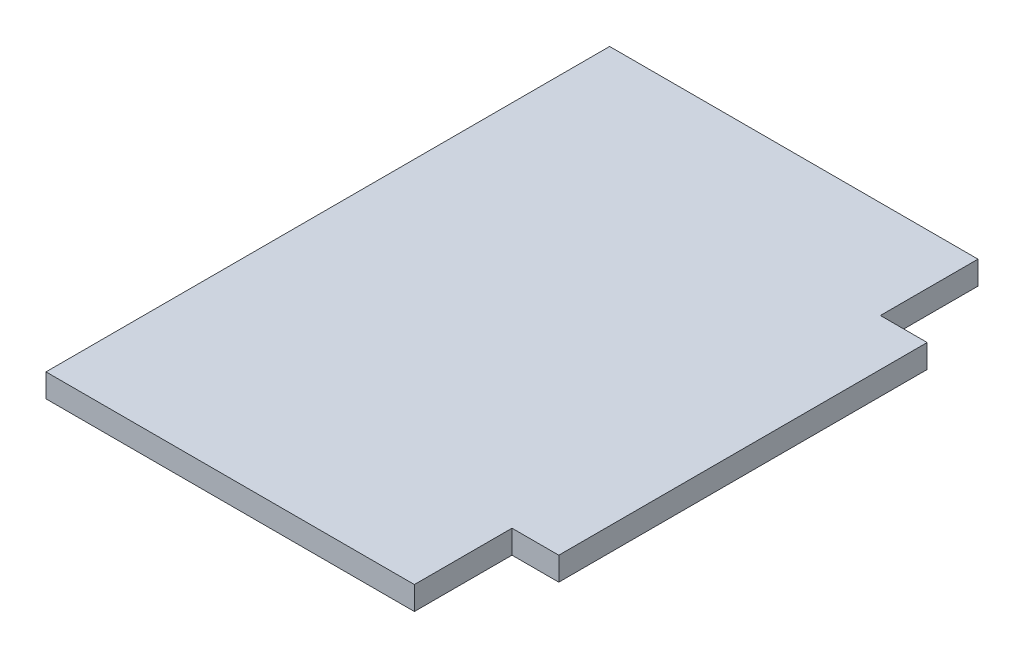
SolidWorks part; units mm, degrees
material "Cedar"
ref_plane "Front Plane" through (0, 0, 0) normal (0, 0, 1) x (1, 0, 0)
ref_plane "Top Plane" through (0, 0, 0) normal (0, 1, 0) x (1, 0, 0)
ref_plane "Right Plane" through (0, 0, 0) normal (1, 0, 0) x (0, 0, -1)
sketch "Sketch1" plane through (0, 0, 0) normal (0, 1, 0) x (1, 0, 0)
  line L0 (-25, 13.25) -> (25, 13.25)
  line L1 (25, 13.25) -> (25, 0)
  line L2 (25, 0) -> (31.35, 0)
  line L3 (31.35, 0) -> (31.35, -50)
  line L4 (31.35, -50) -> (25, -50)
  line L5 (25, -50) -> (25, -63.25)
  line L6 (25, -63.25) -> (-25, -63.25)
  line L7 (-25, -63.25) -> (-25, -50)
  line L8 (-25, -50) -> (-31.35, -50)
  line L9 (-31.35, -50) -> (-31.35, 0)
  line L10 (-31.35, 0) -> (-25, 0)
  line L11 (-25, 0) -> (-25, 13.25)
  line L12 (-25, 0) -> (-25, -50) construction
  point P11 (0, 13.25)
  point P14 (-31.35, -25)
  dimension "D1" = 6.35
  dimension "D2" = 50
  dimension "D3" = 50
  dimension "D4" = 76.5
extrude "Boss-Extrude1" add sketch "Sketch1" along normal blind 3.175 contours L11 L12 L7 L6 L5 L4 L3 L2 L1 L0
equation "\"length\"= 76.5mm"
equation "\"w_mach\"= 50mm"
equation "\"w_tab\"= 50mm"
equation "\"t_wood\"= 0.125in"
equation "\"t_side\"= 0.25in"
equation "\"D1@Sketch1\"=\"t_side\""
equation "\"D2@Sketch1\"=\"w_tab\""
equation "\"D3@Sketch1\"=\"w_mach\""
equation "\"D4@Sketch1\"=\"length\""
equation "\"D1@Boss-Extrude1\"=\"t_wood\""
